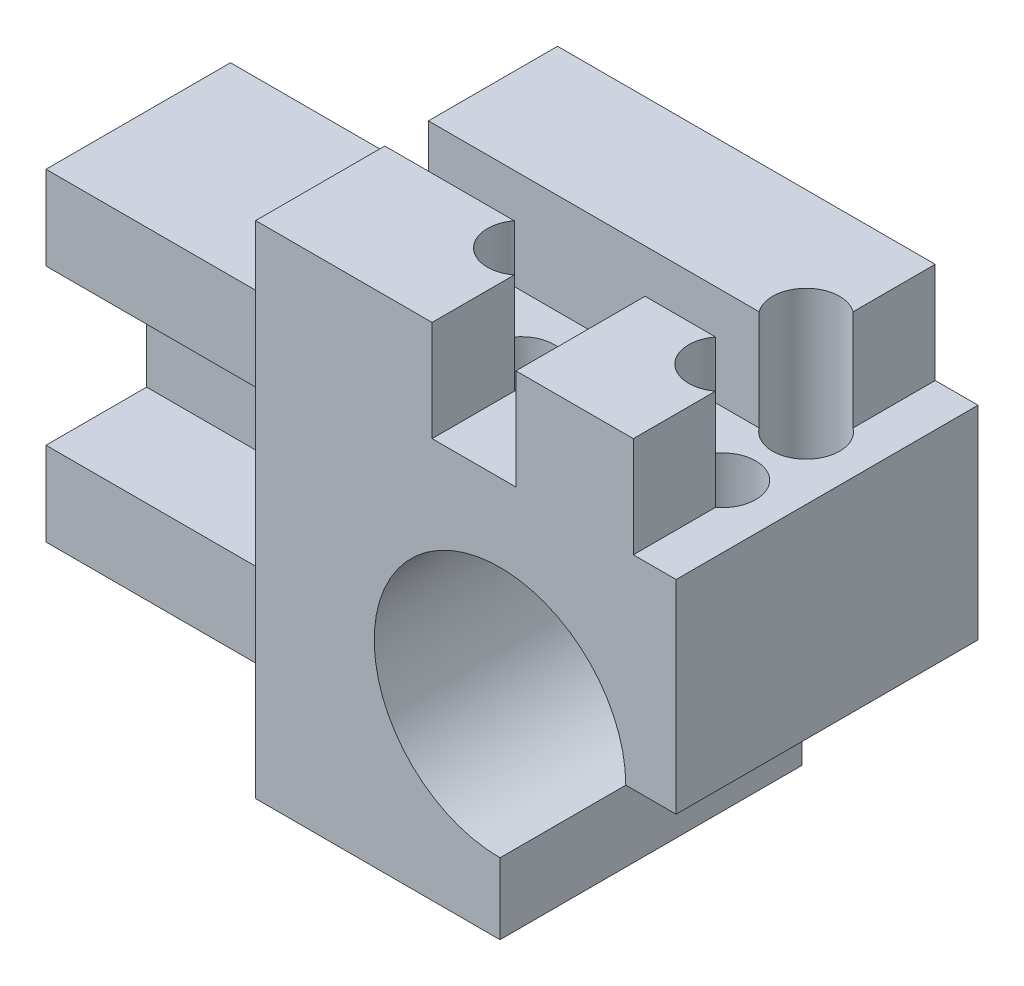
SolidWorks part; units mm, degrees
ref_plane "Front Plane" through (0, 0, 0) normal (0, 0, 1) x (1, 0, 0)
ref_plane "Top Plane" through (0, 0, 0) normal (0, 1, 0) x (1, 0, 0)
ref_plane "Right Plane" through (0, 0, 0) normal (1, 0, 0) x (0, 0, -1)
sketch "Sketch10" plane through (0, 0, 0) normal (0, 0, 1) x (1, 0, 0)
  line L0 (-1.9311, -15.6189) -> (-1.9311, -18.6189)
  line L1 (8.5689, -8.1189) -> (5.5689, -8.1189)
  arc A1 (-1.9311, -18.6189) -> (8.5689, -8.1189) centre (-1.9311, -8.1189) cw
  circle A2 centre (-1.9311, -8.1189) radius 7.5
  dimension "D3" = 15
  dimension "D6" = 3
  dimension "D1" = 1.9311
  dimension "D2" = 8.1189
  dimension "D5" = 90
sketch "Sketch1" plane through (0, 0, 0) normal (0, 0, 1) x (1, 0, 0)
  line L0 (0, 0) -> (8.5689, 0)
  line L1 (8.5689, 0) -> (8.5689, 10)
  line L2 (8.5689, 10) -> (-16.5, 10)
  line L3 (-16.5, 10) -> (-16.5, -19.85)
  line L4 (-16.5, -19.85) -> (0, -19.85)
  line L5 (0, -19.85) -> (0, 0)
  line L6 (8.5689, 0) -> (8.5689, -8.1189)
  line L7 (8.5689, -8.1189) -> (0, -8.1189)
  dimension "D2" = 19.85
  dimension "D3" = 10
  dimension "D4" = 16.5
extrude "Boss-Extrude1" add sketch "Sketch1" along normal mid plane 18 contours L4 L5 L0 L1 L2 L3 | L7 L6 L0 L5
hole_wizard "M3 Clearance Hole1" [suppressed] positions "Sketch2" profile "Sketch3" hole size "M3" standard "ANSI Metric"
sketch "Sketch2" plane through (0, 10, 0) normal (0, 1, 0) x (1, 0, 0)
  line L0 (2.5, 5) -> (17.5, -5) construction
  line L3 (0, 0) -> (10, 0) construction
  point P0 (2.5, -5)
  point P2 (17.5, -5)
  point P4 (17.5, 5)
  point P6 (2.5, 5)
  dimension "D1" = 15
  dimension "D2" = 10
  dimension "D3" = 10
sketch "Sketch3" plane through (2.5, 10, 5) normal (1, 0, 0) x (0, 0, 1)
  line L0 (0, 0) -> (0, 29.85)
  line L1 (0, 29.85) -> (1.7, 29.85)
  line L2 (1.7, 29.85) -> (1.7, 0)
  line L5 (1.7, 0) -> (0, 0)
  line L11 (0, -6.35) -> (0, 107.95) construction
  dimension "Thru Hole Dia." = 3.4
  dimension "Thru Hole Depth" = 29.85
sketch "Sketch4" plane through (0, 0, -9) normal (0, 0, -1) x (-1, 0, 0)
  line L1 (16.5, -19.85) -> (36, -19.85)
  line L2 (16.5, -19.85) -> (16.5, -0.6)
  line L3 (16.5, -0.6) -> (36, -0.6)
  line L4 (36, -19.85) -> (36, -0.6)
  line L5 (26.25, -0.6) -> (26.25, -19.85) construction
  line L6 (16.5, -10.225) -> (36, -10.225) construction
  point P232 (26.25, -10.225)
  dimension "D1" = 36
  dimension "D2" = 19.25
extrude "Boss-Extrude2" add sketch "Sketch4" against normal blind 5
sketch "Sketch5" plane through (0, 0, -4) normal (0, 0, 1) x (1, 0, 0)
  line L0 (-16.5, -0.6) -> (-16.5, -19.85) construction
  line L1 (-36, -19.85) -> (-16.5, -19.85)
  line L2 (-36, -19.85) -> (-36, -14.85)
  line L3 (-36, -14.85) -> (-16.5, -14.85)
  line L4 (-16.5, -19.85) -> (-16.5, -14.85)
  line L5 (-26.25, -14.85) -> (-26.25, -19.85) construction
  line L6 (-36, -17.35) -> (-16.5, -17.35) construction
  line L8 (-16.5, 10) -> (-16.5, -19.85) construction
  line L9 (-36, -0.6) -> (-16.5, -0.6)
  line L10 (-36, -0.6) -> (-36, -5.6)
  line L11 (-36, -5.6) -> (-16.5, -5.6)
  line L12 (-16.5, -0.6) -> (-16.5, -5.6)
  line L13 (-26.25, -5.6) -> (-26.25, -0.6) construction
  line L14 (-36, -3.1) -> (-16.5, -3.1) construction
  point P184 (-26.25, -17.35)
  point P228 (-26.25, -3.1)
  dimension "D1" = 9.25
extrude "Boss-Extrude3" add sketch "Sketch5" along normal blind 6
sketch "Sketch6" plane through (0, 0, -4) normal (0, 0, 1) x (1, 0, 0)
  line L0 (-28, -10.225) -> (-26, -10.225) construction
  line L1 (-28, -8.475) -> (-26, -8.475)
  line L2 (-28, -11.975) -> (-26, -11.975)
  line L3 (-36, -10.225) -> (-28, -10.225) construction
  line L4 (-36, -14.85) -> (-36, -5.6) construction
  line L5 (-16.5, -5.6) -> (-16.5, -14.85) construction
  arc A0 (-28, -8.475) -> (-28, -11.975) centre (-28, -10.225) ccw
  arc A1 (-26, -11.975) -> (-26, -8.475) centre (-26, -10.225) ccw
  point P2 (-27, -10.225)
  dimension "D1" = 3.5
  dimension "D2" = 2
  dimension "D3" = 10.5
extrude "Cut-Extrude1" cut sketch "Sketch6" against normal blind 6
sketch "Sketch7" plane through (0, 10, 0) normal (0, 1, 0) x (1, 0, 0)
  line L1 (-7.1811, -2.5) -> (4.8189, -2.5) construction
  line L2 (-7.1811, -2.5) -> (-7.1811, 2.5) construction
  line L3 (-7.1811, 2.5) -> (4.8189, 2.5) construction
  line L4 (4.8189, -2.5) -> (4.8189, 2.5) construction
  line L5 (-1.1811, 2.5) -> (-1.1811, -2.5) construction
  line L6 (-7.1811, 0) -> (4.8189, 0) construction
  circle A1 centre (4.8189, 2.5) radius 2
  circle A2 centre (4.8189, -2.5) radius 2
  circle A3 centre (-7.1811, -2.5) radius 2
  point P140 (-1.1811, 0)
  dimension "D3" = 4
  dimension "D1" = 4.8189
  dimension "D2" = 12
  dimension "D4" = 5
extrude "Cut-Extrude2" cut sketch "Sketch7" against normal blind 10
sketch "Sketch8" plane through (0, 10, 0) normal (0, 1, 0) x (1, 0, 0)
  line L7 (6.0189, 1.3) -> (6.0189, 9)
  line L8 (6.0189, 9) -> (8.5689, 9)
  line L9 (8.5689, 9) -> (8.5689, -9)
  line L10 (8.5689, -9) -> (6.0189, -9)
  line L12 (6.0189, -9) -> (6.0189, -1.3)
  line L15 (-16.5, -1.3) -> (-5.9811, -1.3)
  line L16 (6.0189, 1.3) -> (4.8189, 2.5) construction
  line L17 (6.0189, -1.3) -> (4.8189, -2.5) construction
  line L18 (-16.5, -9) -> (-16.5, 9) construction
  line L19 (-5.9811, -1.3) -> (-5.9811, -9)
  line L20 (-5.9811, -9) -> (-0.9811, -9)
  line L21 (-0.9811, -9) -> (-0.9811, -1.3)
  line L22 (-0.9811, -1.3) -> (6.0189, -1.3)
  line L23 (-16.5, -1.3) -> (-16.5, 1.3)
  line L24 (-16.5, 1.3) -> (6.0189, 1.3)
  line L25 (-5.9811, -1.3) -> (-7.1811, -2.5) construction
  line L26 (8.5689, -9) -> (-16.5, -9) construction
  dimension "D1" = 45
  dimension "D2" = 1.2
  dimension "D3" = 5
extrude "Cut-Extrude3" cut sketch "Sketch8" against normal blind 6
sketch "Sketch11" plane through (0, 0, 0) normal (0, 0, 1) x (1, 0, 0)
  line L0 (-16.5, -19.85) -> (0, -19.85) construction
  line L2 (-1.9311, -8.1189) -> (8.5689, -8.1189)
  line L3 (-1.9311, -8.1189) -> (-1.9311, -19.85)
  line L9 (-1.9311, -19.85) -> (8.5689, -19.85)
  line L10 (8.5689, -8.1189) -> (8.5689, -19.85)
  line L11 (3.3189, -19.85) -> (3.3189, -8.1189) construction
  line L12 (-1.9311, -13.9845) -> (8.5689, -13.9845) construction
  circle A2 centre (-1.9311, -8.1189) radius 7.5
  point P283 (3.3189, -13.9845)
extrude "Cut-Extrude5" cut sketch "Sketch11" against normal through all both and the other way through all contours L2 A2 L3 | L3 A2 L2 | A2 L3 L9 L10 L2
ref_plane "Plane1" through (0, 0, 0) normal (0, 0, 1) x (1, 0, 0)
mirror "Mirror1" [suppressed] about plane through (0, 0, 0) normal (1, 0, 0)
delete or keep bodies "Body-Delete/Keep 2" [suppressed] type delete bodies bodies 113
